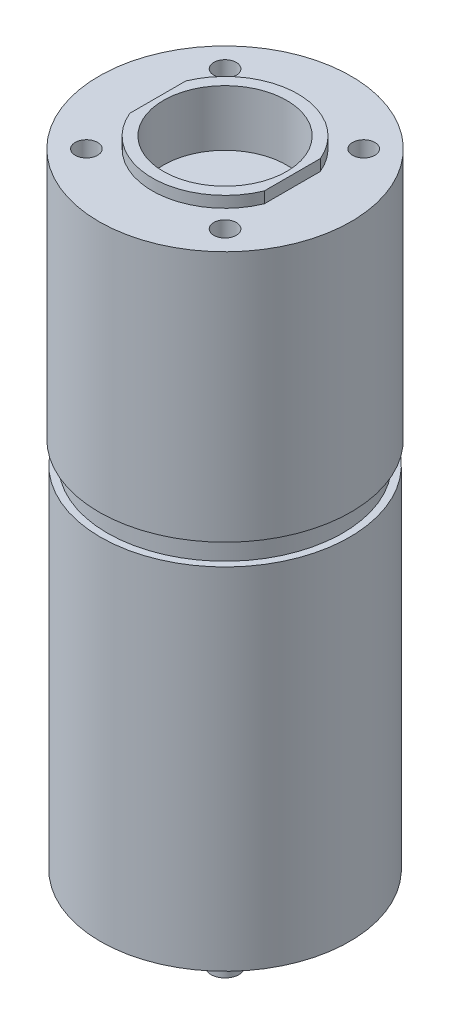
SolidWorks part; units mm, degrees
ref_plane "Front Plane" through (0, 0, 0) normal (0, 0, 1) x (1, 0, 0)
ref_plane "Top Plane" through (0, 0, 0) normal (0, 1, 0) x (1, 0, 0)
ref_plane "Right Plane" through (0, 0, 0) normal (1, 0, 0) x (0, 0, -1)
sketch "Sketch1" plane through (0, 0, 0) normal (0, 0, 1) x (1, 0, 0)
  line L0 (0, 0) -> (0, -56.4963) construction
  line L1 (0, 0) -> (-13, 0)
  line L2 (-13, 0) -> (-13, -2)
  line L3 (-13, -2) -> (-22.5, -2)
  line L4 (-22.5, -2) -> (-22.5, -46.9)
  line L5 (-22.5, -46.9) -> (-21, -46.9)
  line L6 (-21, -46.9) -> (-21, -50.9)
  line L7 (-21, -50.9) -> (-22.25, -50.9)
  line L8 (-22.25, -50.9) -> (-22.25, -113.4)
  line L9 (-22.25, -113.4) -> (-6, -113.4)
  line L10 (-6, -113.4) -> (-6, -118.4)
  line L11 (-6, -118.4) -> (-2.5, -118.4)
  line L12 (-2.5, -118.4) -> (-2.5, -128.4)
  line L13 (-2.5, -128.4) -> (0, -128.4)
  line L14 (0, 0) -> (0, -128.4)
  point P12 (-6, -115.9)
  point P15 (-14.125, -113.4)
  dimension "D1" = 13
  dimension "D2" = 22.5
  dimension "D3" = 22.25
  dimension "D4" = 21
  dimension "D5" = 6
  dimension "D6" = 2
  dimension "D7" = 4
  dimension "D8" = 44.9
  dimension "D9" = 62.5
  dimension "D10" = 5
  dimension "D11" = 2.5
  dimension "D12" = 10
revolve "Revolve1" add sketch "Sketch1" angle 360 about L0
sketch "Sketch2" plane through (0, 0, 0) normal (0, 1, 0) x (1, 0, 0)
  circle A0 centre (0, 0) radius 11
  dimension "D1" = 22
extrude "Cut-Extrude1" cut sketch "Sketch2" against normal blind 10
sketch "Sketch3" plane through (0, 0, 0) normal (0, 1, 0) x (1, 0, 0)
  line L0 (0, 16.7871) -> (0, -16.7871) construction
  line L1 (-12, 16.7871) -> (-12, -16.7871)
  line L2 (12, 16.7871) -> (12, -16.7871)
  line L3 (-12, 16.7871) -> (-17, 16.7871)
  line L4 (-17, 16.7871) -> (-17, -16.7871)
  line L5 (-17, -16.7871) -> (-12, -16.7871)
  line L6 (12, 16.7871) -> (17, 16.7871)
  line L7 (17, 16.7871) -> (17, -16.7871)
  line L8 (17, -16.7871) -> (12, -16.7871)
  point P5 (0, 0)
  dimension "D3" = 5
  dimension "D4" = 5
  dimension "D5" = 33.5742
  dimension "D1" = 12
  dimension "D2" = 12
extrude "Cut-Extrude2" cut sketch "Sketch3" against normal blind 2
sketch "Sketch4" plane through (0, -2, 0) normal (0, 1, 0) x (1, 0, 0)
  line L0 (0, 23.9681) -> (0, -23.9681) construction
  line L1 (-19.5913, 19.5913) -> (19.5913, -19.5913) construction
  circle A0 centre (-12.3744, 12.3744) radius 2
  circle A1 centre (12.3744, 12.3744) radius 2
  circle A2 centre (12.3744, -12.3744) radius 2
  circle A3 centre (-12.3744, -12.3744) radius 2
  point P4 (0, 0)
  point P9 (0, 0)
  point P20 (0, 0)
  dimension "D2" = 4
  dimension "D1" = 17.5
  dimension "D4" = 45
  dimension "D3" = 4
extrude "Cut-Extrude3" cut sketch "Sketch4" against normal blind 9
